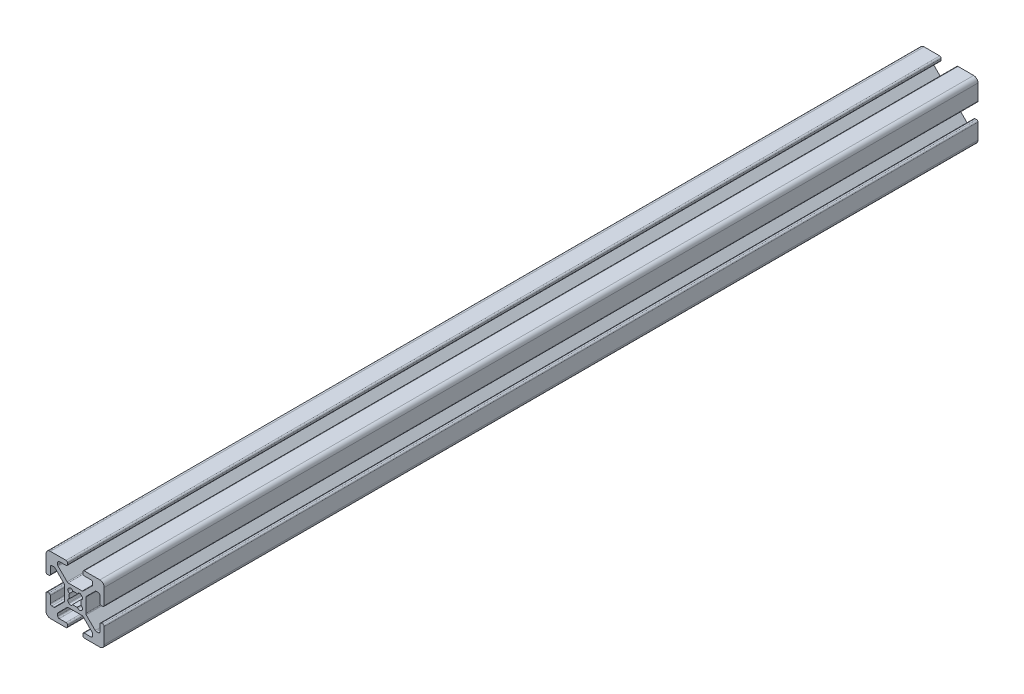
SolidWorks part; units mm, degrees
material "6105-T5 Aluminum"
ref_plane "Front Plane" through (0, 0, 0) normal (0, 0, 1) x (1, 0, 0)
ref_plane "Top Plane" through (0, 0, 0) normal (0, 1, 0) x (1, 0, 0)
ref_plane "Right Plane" through (0, 0, 0) normal (1, 0, 0) x (0, 0, -1)
sketch "Sketch1" plane through (0, 0, 0) normal (0, 0, 1) x (1, 0, 0)
  line L0 (9.492, 2.63) -> (9.008, 2.63)
  line L1 (8.5, 3.138) -> (8.5, 5.487)
  line L2 (10, 3.138) -> (10, 8.5)
  line L3 (3.655, -2.3839) -> (3.655, 2.3839)
  line L4 (7.2661, 5.995) -> (7.992, 5.995)
  line L5 (6.9069, 5.8462) -> (3.8038, 2.7431)
  line L6 (9.492, -2.63) -> (9.008, -2.63)
  line L7 (10, -3.138) -> (10, -8.5)
  line L8 (8.5, -3.138) -> (8.5, -5.487)
  line L9 (7.2661, -5.995) -> (7.992, -5.995)
  line L10 (6.9069, -5.8462) -> (3.8038, -2.7431)
  line L11 (2.1249, -2.3045) -> (2.3045, -2.1249)
  line L12 (-2.63, 9.492) -> (-2.63, 9.008)
  line L13 (-3.138, 10) -> (-8.5, 10)
  line L14 (-3.138, 8.5) -> (-5.487, 8.5)
  line L15 (2.3839, 3.655) -> (-2.3839, 3.655)
  line L16 (-5.995, 7.2661) -> (-5.995, 7.992)
  line L17 (-5.8462, 6.9069) -> (-2.7431, 3.8038)
  line L18 (2.63, 9.492) -> (2.63, 9.008)
  line L19 (3.138, 10) -> (8.5, 10)
  line L20 (3.138, 8.5) -> (5.487, 8.5)
  line L21 (5.995, 7.2661) -> (5.995, 7.992)
  line L22 (5.8462, 6.9069) -> (2.7431, 3.8038)
  line L23 (2.3045, 2.1249) -> (2.1249, 2.3045)
  line L24 (-9.492, -2.63) -> (-9.008, -2.63)
  line L25 (-10, -3.138) -> (-10, -8.5)
  line L26 (-8.5, -3.138) -> (-8.5, -5.487)
  line L27 (-3.655, 2.3839) -> (-3.655, -2.3839)
  line L28 (-7.2661, -5.995) -> (-7.992, -5.995)
  line L29 (-6.9069, -5.8462) -> (-3.8038, -2.7431)
  line L30 (-9.492, 2.63) -> (-9.008, 2.63)
  line L31 (-10, 3.138) -> (-10, 8.5)
  line L32 (-8.5, 3.138) -> (-8.5, 5.487)
  line L33 (-7.2661, 5.995) -> (-7.992, 5.995)
  line L34 (-6.9069, 5.8462) -> (-3.8038, 2.7431)
  line L35 (-2.1249, 2.3045) -> (-2.3045, 2.1249)
  line L36 (2.63, -9.492) -> (2.63, -9.008)
  line L37 (3.138, -10) -> (8.5, -10)
  line L38 (3.138, -8.5) -> (5.487, -8.5)
  line L39 (-2.3839, -3.655) -> (2.3839, -3.655)
  line L40 (5.995, -7.2661) -> (5.995, -7.992)
  line L41 (5.8462, -6.9069) -> (2.7431, -3.8038)
  line L42 (-2.63, -9.492) -> (-2.63, -9.008)
  line L43 (-3.138, -10) -> (-8.5, -10)
  line L44 (-3.138, -8.5) -> (-5.487, -8.5)
  line L45 (-5.995, -7.2661) -> (-5.995, -7.992)
  line L46 (-5.8462, -6.9069) -> (-2.7431, -3.8038)
  line L47 (-2.3045, -2.1249) -> (-2.1249, -2.3045)
  arc A0 (-0.804, -1.9351) -> (0.804, -1.9351) centre (0, 0) ccw
  arc A1 (8.5, 5.487) -> (7.992, 5.995) centre (7.992, 5.487) ccw
  arc A2 (7.2661, 5.995) -> (6.9069, 5.8462) centre (7.2661, 5.487) ccw
  arc A3 (3.8038, 2.7431) -> (3.655, 2.3839) centre (4.163, 2.3839) ccw
  arc A4 (3.655, -2.3839) -> (3.8038, -2.7431) centre (4.163, -2.3839) ccw
  arc A5 (6.9069, -5.8462) -> (7.2661, -5.995) centre (7.2661, -5.487) ccw
  arc A6 (7.992, -5.995) -> (8.5, -5.487) centre (7.992, -5.487) ccw
  arc A7 (9.008, -2.63) -> (8.5, -3.138) centre (9.008, -3.138) ccw
  arc A8 (10, -3.138) -> (9.492, -2.63) centre (9.492, -3.138) ccw
  arc A9 (9.492, 2.63) -> (10, 3.138) centre (9.492, 3.138) ccw
  arc A10 (8.5, 3.138) -> (9.008, 2.63) centre (9.008, 3.138) ccw
  arc A11 (0.804, -1.9351) -> (2.1249, -2.3045) centre (1.5684, -1.748) ccw
  arc A12 (2.3045, -2.1249) -> (1.9351, -0.804) centre (1.748, -1.5684) ccw
  arc A13 (-2.63, 9.492) -> (-3.138, 10) centre (-3.138, 9.492) ccw
  arc A14 (-3.138, 8.5) -> (-2.63, 9.008) centre (-3.138, 9.008) ccw
  arc A15 (1.9351, -0.804) -> (1.9351, 0.804) centre (0, 0) ccw
  arc A16 (-2.7431, 3.8038) -> (-2.3839, 3.655) centre (-2.3839, 4.163) ccw
  arc A17 (-5.487, 8.5) -> (-5.995, 7.992) centre (-5.487, 7.992) ccw
  arc A18 (-5.995, 7.2661) -> (-5.8462, 6.9069) centre (-5.487, 7.2661) ccw
  arc A19 (2.63, 9.008) -> (3.138, 8.5) centre (3.138, 9.008) ccw
  arc A20 (3.138, 10) -> (2.63, 9.492) centre (3.138, 9.492) ccw
  arc A21 (5.995, 7.992) -> (5.487, 8.5) centre (5.487, 7.992) ccw
  arc A22 (5.8462, 6.9069) -> (5.995, 7.2661) centre (5.487, 7.2661) ccw
  arc A23 (2.3839, 3.655) -> (2.7431, 3.8038) centre (2.3839, 4.163) ccw
  arc A24 (1.9351, 0.804) -> (2.3045, 2.1249) centre (1.748, 1.5684) ccw
  arc A25 (2.1249, 2.3045) -> (0.804, 1.9351) centre (1.5684, 1.748) ccw
  arc A26 (-9.492, -2.63) -> (-10, -3.138) centre (-9.492, -3.138) ccw
  arc A27 (-8.5, -3.138) -> (-9.008, -2.63) centre (-9.008, -3.138) ccw
  arc A28 (0.804, 1.9351) -> (-0.804, 1.9351) centre (0, 0) ccw
  arc A29 (-3.8038, -2.7431) -> (-3.655, -2.3839) centre (-4.163, -2.3839) ccw
  arc A30 (-8.5, -5.487) -> (-7.992, -5.995) centre (-7.992, -5.487) ccw
  arc A31 (-7.2661, -5.995) -> (-6.9069, -5.8462) centre (-7.2661, -5.487) ccw
  arc A32 (-9.008, 2.63) -> (-8.5, 3.138) centre (-9.008, 3.138) ccw
  arc A33 (-10, 3.138) -> (-9.492, 2.63) centre (-9.492, 3.138) ccw
  arc A34 (-7.992, 5.995) -> (-8.5, 5.487) centre (-7.992, 5.487) ccw
  arc A35 (-6.9069, 5.8462) -> (-7.2661, 5.995) centre (-7.2661, 5.487) ccw
  arc A36 (-3.655, 2.3839) -> (-3.8038, 2.7431) centre (-4.163, 2.3839) ccw
  arc A37 (-0.804, 1.9351) -> (-2.1249, 2.3045) centre (-1.5684, 1.748) ccw
  arc A38 (-2.3045, 2.1249) -> (-1.9351, 0.804) centre (-1.748, 1.5684) ccw
  arc A39 (2.63, -9.492) -> (3.138, -10) centre (3.138, -9.492) ccw
  arc A40 (3.138, -8.5) -> (2.63, -9.008) centre (3.138, -9.008) ccw
  arc A41 (-1.9351, 0.804) -> (-1.9351, -0.804) centre (0, 0) ccw
  arc A42 (2.7431, -3.8038) -> (2.3839, -3.655) centre (2.3839, -4.163) ccw
  arc A43 (5.487, -8.5) -> (5.995, -7.992) centre (5.487, -7.992) ccw
  arc A44 (5.995, -7.2661) -> (5.8462, -6.9069) centre (5.487, -7.2661) ccw
  arc A45 (-2.63, -9.008) -> (-3.138, -8.5) centre (-3.138, -9.008) ccw
  arc A46 (-3.138, -10) -> (-2.63, -9.492) centre (-3.138, -9.492) ccw
  arc A47 (-5.995, -7.992) -> (-5.487, -8.5) centre (-5.487, -7.992) ccw
  arc A48 (-5.8462, -6.9069) -> (-5.995, -7.2661) centre (-5.487, -7.2661) ccw
  arc A49 (-2.3839, -3.655) -> (-2.7431, -3.8038) centre (-2.3839, -4.163) ccw
  arc A50 (-1.9351, -0.804) -> (-2.3045, -2.1249) centre (-1.748, -1.5684) ccw
  arc A51 (-2.1249, -2.3045) -> (-0.804, -1.9351) centre (-1.5684, -1.748) ccw
  arc A52 (10, 8.5) -> (8.5, 10) centre (8.5, 8.5) ccw
  arc A53 (8.5, -10) -> (10, -8.5) centre (8.5, -8.5) ccw
  arc A54 (-10, -8.5) -> (-8.5, -10) centre (-8.5, -8.5) ccw
  arc A55 (-8.5, 10) -> (-10, 8.5) centre (-8.5, 8.5) ccw
extrude "Extrude1" add sketch "Sketch1" against normal blind 300
